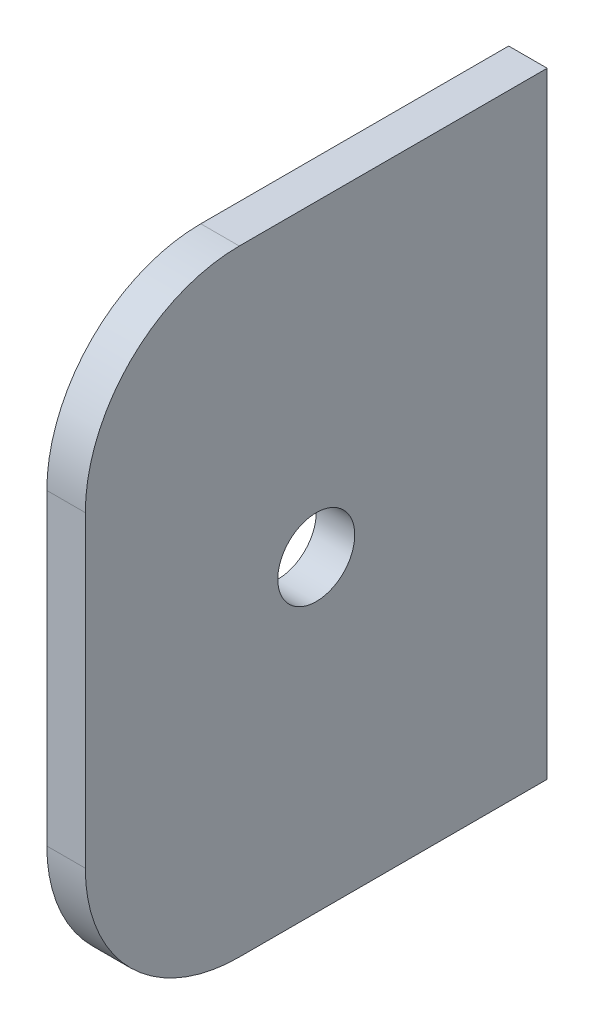
SolidWorks part; units mm, degrees
ref_plane "Front Plane" through (0, 0, 0) normal (0, 0, 1) x (1, 0, 0)
ref_plane "Top Plane" through (0, 0, 0) normal (0, 1, 0) x (1, 0, 0)
ref_plane "Right Plane" through (0, 0, 0) normal (1, 0, 0) x (0, 0, -1)
sketch "Sketch1" plane through (0, 0, 0) normal (0, 0, 1) x (1, 0, 0)
  line L1 (19.05, 1.016) -> (15.875, 1.016)
  line L2 (19.05, 1.016) -> (19.05, -49.784)
  line L3 (19.05, -49.784) -> (15.875, -49.784)
  line L4 (15.875, 1.016) -> (15.875, -49.784)
  dimension "D1" = 50.8
  dimension "D2" = 3.175
extrude "Boss-Extrude1" add sketch "Sketch1" along normal blind 38.1 contours L4 L3 L2 L1
sketch "Sketch3" plane through (15.875, 0, 0) normal (-1, 0, 0) x (0, 0, 1)
  line L0 (38.1, 1.016) -> (38.1, -49.784) construction
  line L1 (38.1, 1.016) -> (0, 1.016) construction
  circle A0 centre (19.05, -24.384) radius 3.175
  point P4 (38.1, -24.384)
  point P10 (19.05, 1.016)
  dimension "D1" = 6.35
extrude "Cut-Extrude1" cut sketch "Sketch3" against normal blind 38.1
fillet "Fillet1" radius 12.7 2 edges at (17.4625, 1.016, 38.1) (17.4625, -49.784, 38.1)
